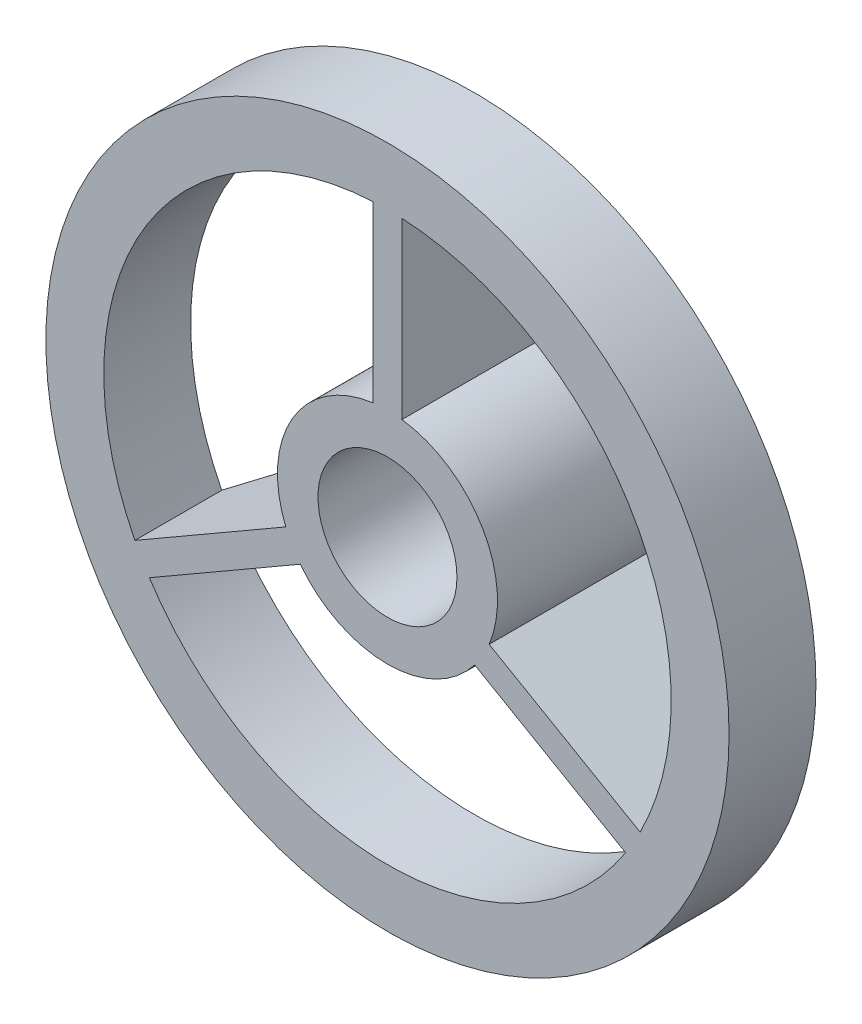
SolidWorks part; units mm, degrees
ref_plane "Front Plane" through (0, 0, 0) normal (0, 0, 1) x (1, 0, 0)
ref_plane "Top Plane" through (0, 0, 0) normal (0, 1, 0) x (1, 0, 0)
ref_plane "Right Plane" through (0, 0, 0) normal (1, 0, 0) x (0, 0, -1)
sketch "Sketch1" plane through (0, 0, 0) normal (0, 0, 1) x (1, 0, 0)
  circle A0 centre (0, 0) radius 1.2
  circle A1 centre (0, 0) radius 1.9
  dimension "D1" = 2.4
  dimension "D2" = 0.7
extrude "Boss-Extrude1" add sketch "Sketch1" along normal blind 3.5
sketch "Sketch3" plane through (0, 0, 3.5) normal (0, 0, 1) x (1, 0, 0)
  circle A1 centre (0, 0) radius 5.9
  circle A2 centre (0, 0) radius 4.9
  circle A3 centre (0, 0) radius 4.9
  dimension "D1" = 3
  dimension "D2" = 1
extrude "Boss-Extrude3" add sketch "Sketch3" against normal blind 1.5 separate body
sketch "Sketch8" plane through (0, 0, 0) normal (1, 0, 0) x (0, 0, -1)
  line L0 (-2, 4.9) -> (0, 1.9)
  line L1 (-2, -5.9) -> (-2, 5.9) construction
  line L2 (-2, -4.9) -> (-2, 4.9) construction
  line L3 (0, -1.9) -> (0, 1.9) construction
  line L4 (0, 1.9) -> (-3.5, 1.9) construction
  line L5 (-3.5, 1.9) -> (-3.5, -1.9) construction
  line L6 (-3.5, 1.9) -> (-3.5, 4.9)
  line L7 (-3.5, 4.9) -> (-3.5, -4.9) construction
  line L8 (-2, 4.9) -> (-3.5, 4.9)
  line L9 (0, 1.7) -> (-3.5, 1.7)
  line L10 (0, 1.9) -> (0, 1.7)
  line L11 (-3.5, 1.9) -> (-3.5, 1.7)
  dimension "D1" = 0.2
extrude "Boss-Extrude4" add sketch "Sketch8" along normal mid plane 0.5
pattern_circular "CirPattern1" count 3 over 360 about axis through (0, 0, 0) along (0, 0, 1) of "Boss-Extrude4"
